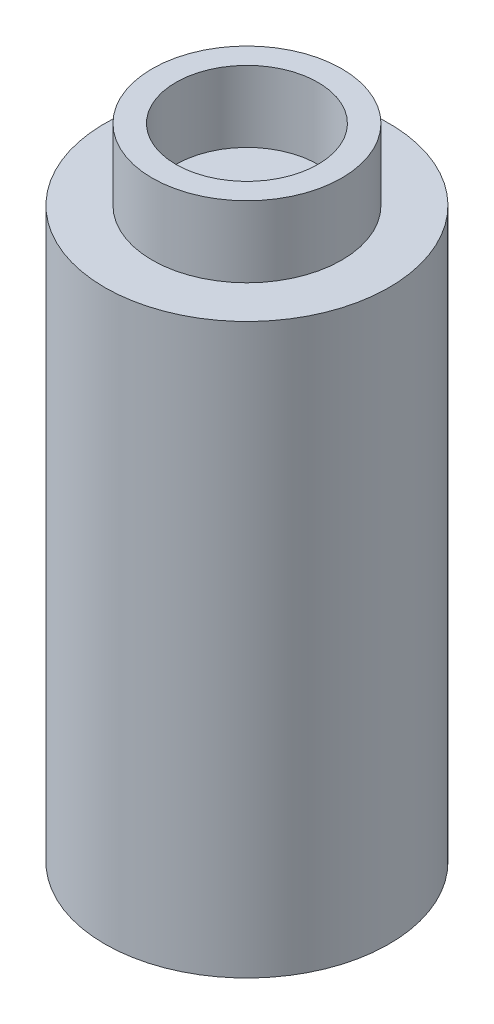
SolidWorks part; units mm, degrees
ref_plane "Front Plane" through (0, 0, 0) normal (0, 0, 1) x (1, 0, 0)
ref_plane "Top Plane" through (0, 0, 0) normal (0, 1, 0) x (1, 0, 0)
ref_plane "Right Plane" through (0, 0, 0) normal (1, 0, 0) x (0, 0, -1)
sketch "Sketch2" plane through (0, 0, 0) normal (0, 1, 0) x (1, 0, 0)
  circle A0 centre (0, 0) radius 6
  dimension "D1" = 12
extrude "Boss-Extrude1" add sketch "Sketch2" along normal blind 24
sketch "Sketch3" plane through (0, 24, 0) normal (0, 1, 0) x (1, 0, 0)
  circle A0 centre (0, 0) radius 4
  dimension "D1" = 8
extrude "Boss-Extrude2" add sketch "Sketch3" along normal blind 3
sketch "Sketch4" plane through (0, 27, 0) normal (0, 1, 0) x (1, 0, 0)
  circle A0 centre (0, 0) radius 3
  dimension "D1" = 6
extrude "Cut-Extrude1" cut sketch "Sketch4" against normal blind 3
